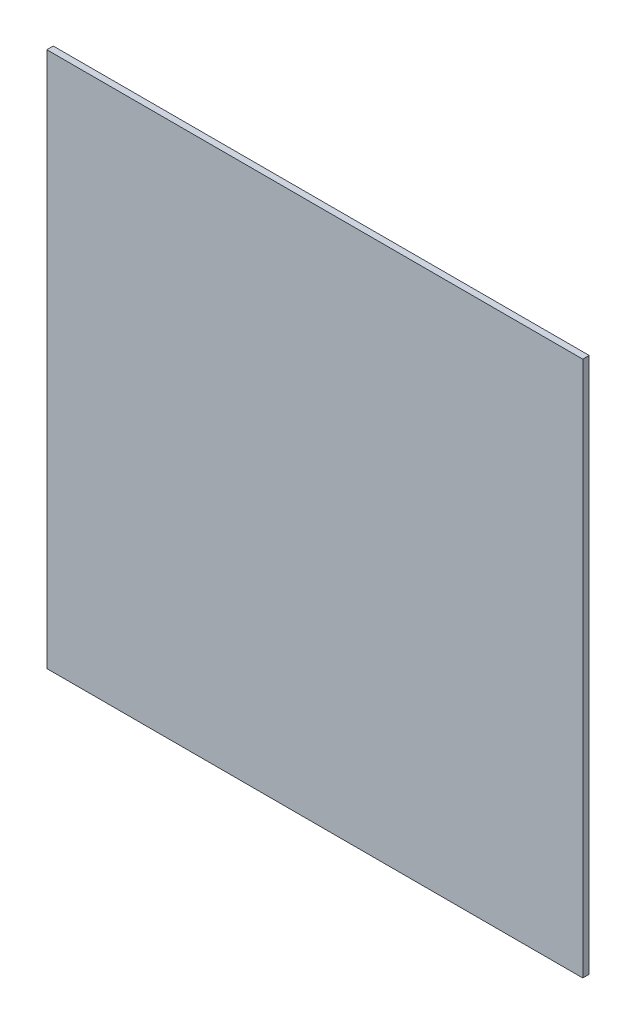
SolidWorks part; units mm, degrees
ref_plane "정면" through (0, 0, 0) normal (0, 0, 1) x (1, 0, 0)
ref_plane "윗면" through (0, 0, 0) normal (0, 1, 0) x (1, 0, 0)
ref_plane "우측면" through (0, 0, 0) normal (1, 0, 0) x (0, 0, -1)
sketch "스케치1" plane through (0, 0, 0) normal (0, 1, 0) x (1, 0, 0)
  line L1 (0, 0) -> (250, 0)
  line L2 (0, 0) -> (0, 3)
  line L3 (0, 3) -> (250, 3)
  line L4 (250, 0) -> (250, 3)
  dimension "D1" = 3
  dimension "D2" = 250
extrude "보스-돌출1" add sketch "스케치1" along normal blind 250
